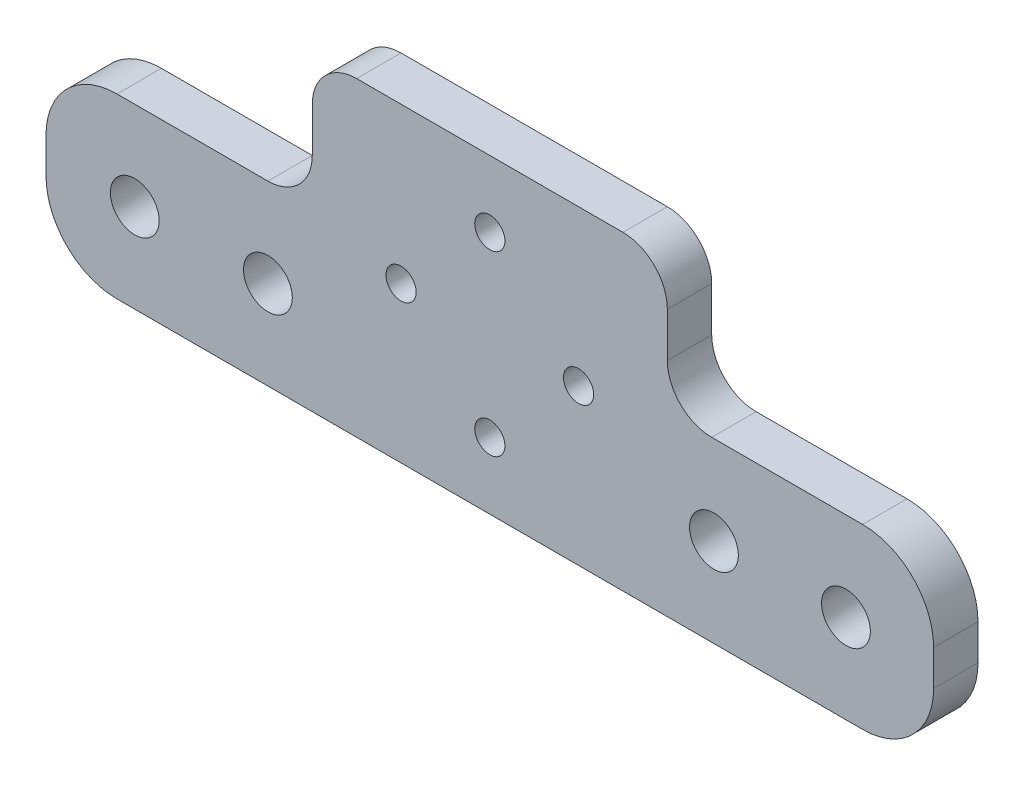
SolidWorks part; units mm, degrees
ref_plane "XY" through (0, 0, 0) normal (0, 0, 1) x (1, 0, 0)
ref_plane "XZ" through (0, 0, 0) normal (0, 1, 0) x (1, 0, 0)
ref_plane "YZ" through (0, 0, 0) normal (1, 0, 0) x (0, 0, -1)
sketch "Sketch1" plane through (0, 0, 0) normal (0, 0, 1) x (1, 0, 0)
  line L0 (0, 0) -> (0, 66.5072) construction
  line L1 (42, 0) -> (-42, 0)
  line L2 (-50, 8) -> (-50, 12)
  line L3 (-42, 20) -> (-25, 20)
  line L4 (-20, 25) -> (-20, 30)
  line L5 (-15, 35) -> (15, 35)
  line L6 (20, 25) -> (20, 30)
  line L7 (42, 20) -> (25, 20)
  line L8 (50, 8) -> (50, 12)
  arc A0 (-25, 20) -> (-20, 25) centre (-25, 25) ccw
  arc A1 (-20, 30) -> (-15, 35) centre (-15, 30) cw
  arc A2 (-42, 0) -> (-50, 8) centre (-42, 8) cw
  arc A3 (-50, 12) -> (-42, 20) centre (-42, 12) cw
  arc A4 (50, 12) -> (42, 20) centre (42, 12) ccw
  arc A5 (42, 0) -> (50, 8) centre (42, 8) ccw
  arc A6 (20, 30) -> (15, 35) centre (15, 30) ccw
  arc A7 (25, 20) -> (20, 25) centre (25, 25) cw
  point P5 (50, 0)
  point P10 (-20, 20)
  point P13 (-20, 35)
  point P16 (-50, 0)
  point P31 (0, 35)
  point P32 (20, 35)
  point P33 (20, 20)
  dimension "D5" = 5
  dimension "D6" = 8
  dimension "D1" = 20
  dimension "D2" = 50
  dimension "D3" = 15
  dimension "D4" = 20
extrude "Boss-Extrude1" add sketch "Sketch1" along normal blind 5
sketch "Sketch2" plane through (0, 0, 5) normal (0, 0, 1) x (1, 0, 0)
  line L0 (-50, 10) -> (50, 10) construction
  line L1 (-50, 12) -> (-50, 8) construction
  line L2 (50, 8) -> (50, 12) construction
  point P6 (-40, 10)
  point P7 (-25, 10)
  point P8 (25.25, 10)
  point P9 (40.125, 10)
  dimension "D1" = 10
  dimension "D2" = 25
  dimension "D3" = 75.25
  dimension "D4" = 90.125
hole_wizard "M5 Clearance Hole1" positions "Sketch3" profile "Sketch4" hole size "M5" standard "ANSI Metric" end condition up to next
sketch "Sketch3" plane through (0, 0, 5) normal (0, 0, 1) x (1, 0, 0)
  point P0 (-40, 10)
  point P3 (-25, 10)
  point P6 (25.25, 10)
  point P9 (40.125, 10)
sketch "Sketch4" plane through (-40, 10, 5) normal (1, 0, 0) x (0, -1, 0)
  line L0 (0, 0) -> (0, 5)
  line L1 (0, 5) -> (2.75, 5)
  line L2 (2.75, 5) -> (2.75, 0)
  line L5 (2.75, 0) -> (0, 0)
  line L11 (0, -6.35) -> (0, 107.95) construction
  dimension "Thru Hole Dia." = 5.5
  dimension "Thru Hole Depth" = 5
sketch "Sketch6" plane through (0, 0, 0) normal (0, 0, -1) x (-1, 0, 0)
  line L0 (0, 7.5) -> (0, 27.5) construction
  line L1 (-15, 35) -> (15, 35) construction
  line L2 (0, 27.5) -> (0, 35) construction
  line L3 (0, 7.5) -> (0, 0) construction
  line L5 (15.2522, 17.5) -> (-19.8251, 17.5) construction
  point P5 (0, 7.5)
  point P6 (0, 27.5)
  point P9 (-10, 17.5)
  point P11 (10, 17.5)
  point P13 (0, 17.5)
  dimension "D1" = 20
  dimension "D2" = 10
  dimension "D3" = 20
hole_wizard "CSK for M3 Flat Head Machine Screw1" positions "Sketch7" profile "Sketch8" countersink size "M3" standard "ANSI Metric" end condition up to next
sketch "Sketch7" plane through (0, 0, 0) normal (0, 0, -1) x (-1, 0, 0)
  point P0 (-10, 17.5)
  point P3 (0, 7.5)
  point P6 (10, 17.5)
  point P9 (0, 27.5)
sketch "Sketch8" plane through (10, 17.5, 0) normal (1, 0, 0) x (0, 1, 0)
  line L0 (0, 0) -> (0, 5)
  line L1 (0, 5) -> (1.7, 5)
  line L2 (1.7, 5) -> (1.7, 1.45)
  line L3 (1.7, 1.45) -> (3.15, 0)
  line L5 (3.15, 0) -> (0, 0)
  line L6 (-1.7, 1.45) -> (-3.15, 0) construction
  line L11 (0, -6.35) -> (0, 107.95) construction
  dimension "Thru Hole Dia." = 3.4
  dimension "Thru Hole Depth" = 5
  dimension "Near C'Sink Dia." = 6.3
  dimension "Near C'Sink Angle" = 90
